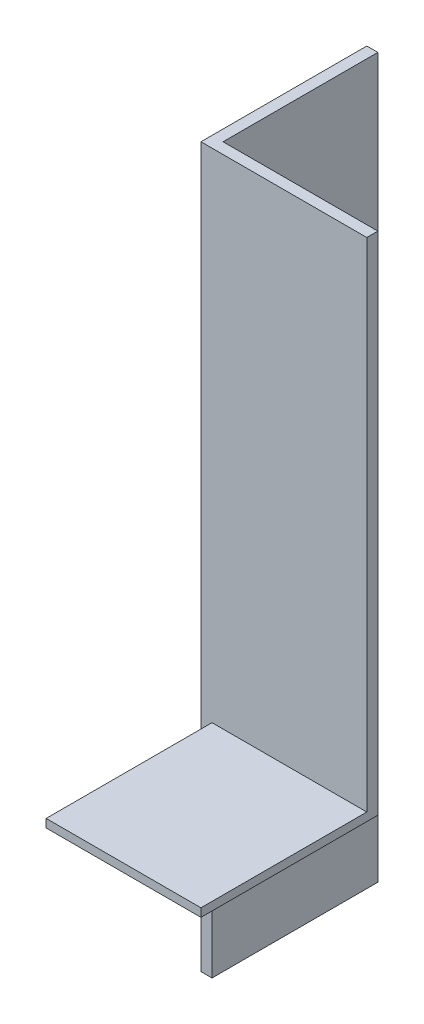
SolidWorks part; units mm, degrees
material "1060 Сплав"
ref_plane "Спереди" through (0, 0, 0) normal (0, 0, 1) x (1, 0, 0)
ref_plane "Сверху" through (0, 0, 0) normal (0, 1, 0) x (1, 0, 0)
ref_plane "Справа" through (0, 0, 0) normal (1, 0, 0) x (0, 0, -1)
sketch "Эскиз1" plane through (0, 0, 0) normal (0, 1, 0) x (1, 0, 0)
  line L0 (0, 0) -> (0, 15)
  line L1 (0, 15) -> (1, 15)
  line L2 (1, 15) -> (1, 1)
  line L3 (1, 1) -> (15, 1)
  line L4 (15, 1) -> (15, 0)
  line L5 (15, 0) -> (0, 0)
  dimension "D1" = 1
  dimension "D2" = 15
extrude "Бобышка-Вытянуть1" add sketch "Эскиз1" along normal blind 65
sketch "Эскиз2" plane through (0, 0, 0) normal (0, 0, 1) x (1, 0, 0)
  line L0 (285, 20) -> (-75, 20) construction
  line L1 (285, 20) -> (-75, 20) construction
sketch "Эскиз5" plane through (0, 0, 0) normal (-1, 0, 0) x (0, 0, 1)
  line L0 (0, 20) -> (-15, 20) construction
  line L1 (0, 65) -> (0, 0) construction
  line L2 (-15, 65) -> (-15, 0) construction
ref_plane "Плоскость1" through (0, 20, 0) normal (0, 1, 0) x (1, 0, 0)
sketch "Эскиз6" plane through (0, 0, 0) normal (0, -1, 0) x (1, 0, 0)
  line L0 (0, 0) -> (15, 0) construction
  line L1 (1, -1) -> (1, 0)
  line L6 (15, 0) -> (0, 0)
  line L7 (0, 0) -> (0, -15)
  line L8 (0, -15) -> (1, -15)
  line L9 (1, -15) -> (1, -1)
  line L10 (1, -1) -> (15, -1)
  line L11 (15, -1) -> (15, 0)
  line L12 (15, 0) -> (1, 0)
  line L16 (1, -1) -> (15, -1)
  line L17 (15, -1) -> (15, 0)
  dimension "D1" = 0
extrude "Вырез-Вытянуть2" cut sketch "Эскиз6" against normal up to surface (20 mm away)
sketch "Эскиз7" plane through (0, 0, -1) normal (0, 0, -1) x (-1, 0, 0)
  line L0 (-1, 20) -> (-15, 20)
  line L1 (-1, 20) -> (-1, 19.25)
  line L2 (-15, 20) -> (-15, 19.25)
  line L3 (-1, 19.25) -> (-15, 19.25)
  dimension "D1" = 0.75
extrude "Бобышка-Вытянуть2" add sketch "Эскиз7" against normal blind 16
